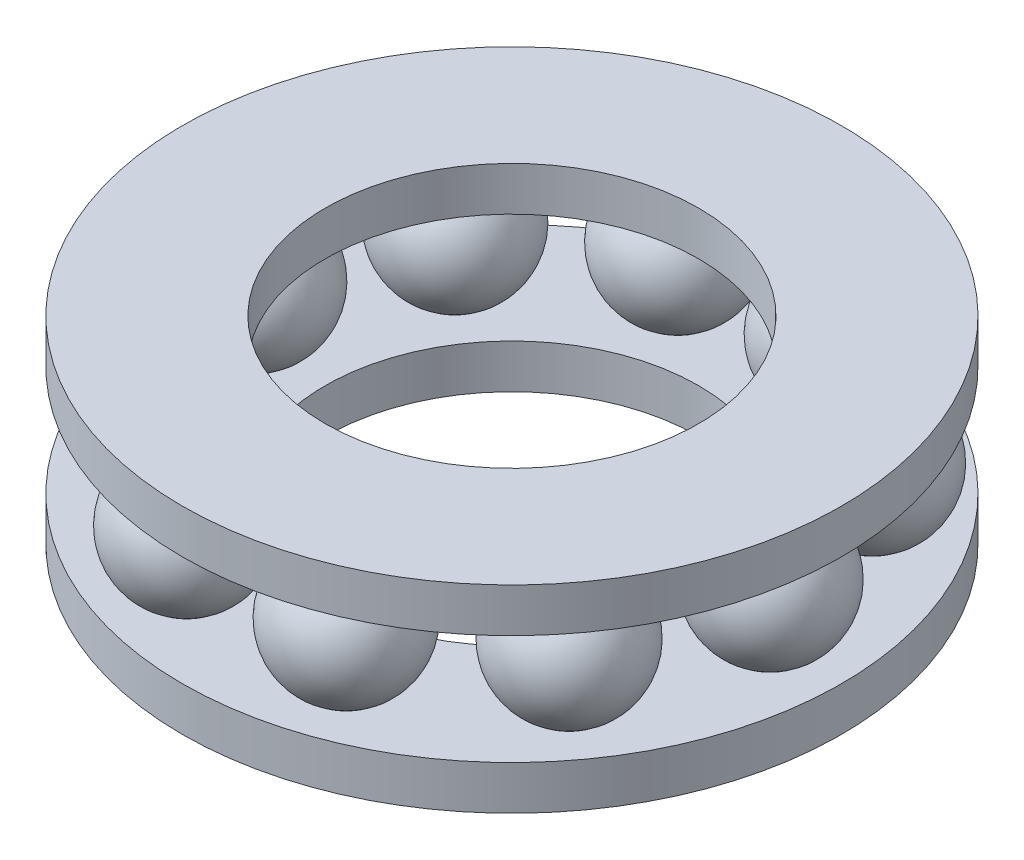
SolidWorks part; units mm, degrees
ref_plane "前视基准面" through (0, 0, 0) normal (0, 0, 1) x (1, 0, 0)
ref_plane "上视基准面" through (0, 0, 0) normal (0, 1, 0) x (1, 0, 0)
ref_plane "右视基准面" through (0, 0, 0) normal (1, 0, 0) x (0, 0, -1)
sketch "草图1" plane through (0, 0, 0) normal (0, 1, 0) x (1, 0, 0)
  circle A0 centre (0, 0) radius 8.5
  circle A1 centre (0, 0) radius 15
  dimension "D1" = 17
  dimension "D2" = 30
extrude "凸台-拉伸1" add sketch "草图1" along normal blind 2
sketch "草图4" plane through (0, 0, 0) normal (0, 0, 1) x (1, 0, 0)
  line L0 (15, 2) -> (-15, 2) construction
  line L1 (9.25, 2) -> (14.25, 2) construction
  line L2 (9.25, 2) -> (9.25, 7) construction
  line L3 (9.25, 7) -> (14.25, 7) construction
  line L4 (14.25, 2) -> (14.25, 7) construction
  line L5 (9.25, 2) -> (14.25, 7) construction
  line L6 (9.25, 7) -> (14.25, 2) construction
  line L7 (8.5, 2) -> (8.5, 7.3206) construction
  line L8 (8.75, 4.5) -> (14.75, 4.5)
  circle A0 centre (11.75, 4.5) radius 3.5355 construction
  arc A2 (8.75, 4.5) -> (14.75, 4.5) centre (11.75, 4.5) ccw
  point P0 (11.75, 4.5)
  dimension "D1" = 0
  dimension "D2" = 11.75
  dimension "D3" = 5
  dimension "D4" = 5
revolve "旋转4" add sketch "草图4" angle 360 about L8
pattern_circular "阵列(圆周)2" count 10 over 360 about axis through (0, 0, 0) along (0, 1, 0) of "旋转4"
pattern_linear "阵列(线性)2" count 2 spacing 7 along (0, 1, 0) of "凸台-拉伸1"
ref_point "点1"
ref_point "点2"
